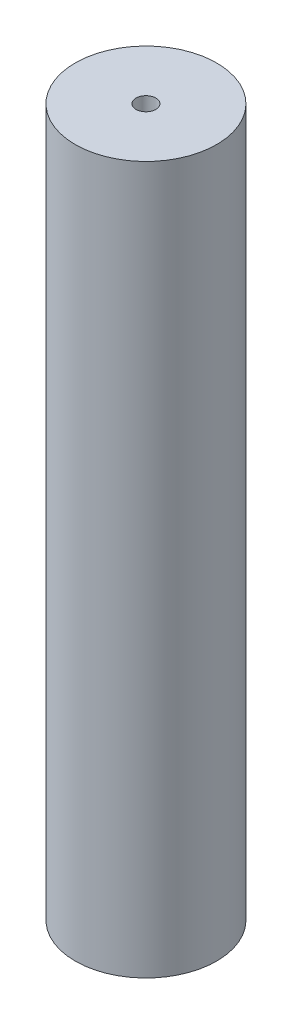
SolidWorks part; units mm, degrees
ref_plane "Спереди" through (0, 0, 0) normal (0, 0, 1) x (1, 0, 0)
ref_plane "Сверху" through (0, 0, 0) normal (0, 1, 0) x (1, 0, 0)
ref_plane "Справа" through (0, 0, 0) normal (1, 0, 0) x (0, 0, -1)
other "Configuration Table"
sketch "Эскиз1" plane through (0, 0, 0) normal (0, 1, 0) x (1, 0, 0)
  circle A0 centre (-1.375, 1.3858) radius 2.5
  circle A1 centre (-1.375, 1.3858) radius 0.35
  dimension "D1" = 5
  dimension "D2" = 0.7
  dimension "D3" = 0
extrude "Бобышка-Вытянуть3" add sketch "Эскиз1" along normal blind 25
